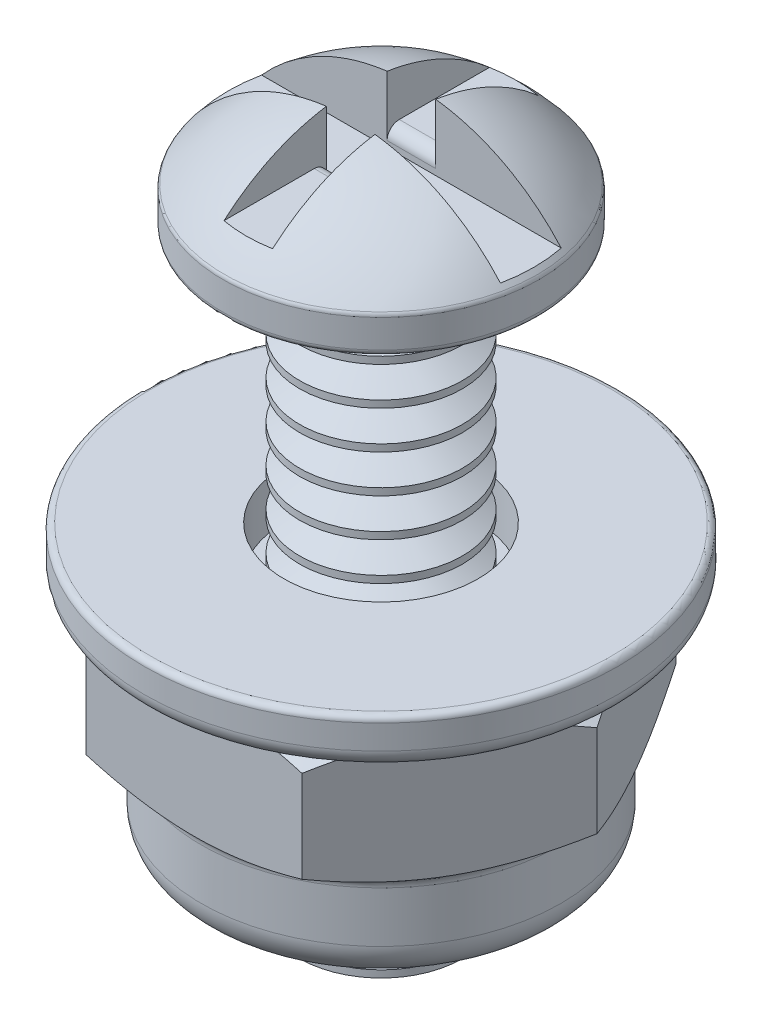
SolidWorks part; units mm, degrees
other "Nut"
other "Screw Body"
other "Washer"
material "Plain Carbon Steel"
ref_plane "Front Plane" through (0, 0, 0) normal (0, 0, 1) x (1, 0, 0)
ref_plane "Top Plane" through (0, 0, 0) normal (0, 1, 0) x (1, 0, 0)
ref_plane "Right Plane" through (0, 0, 0) normal (1, 0, 0) x (0, 0, -1)
sketch "Sketch1" plane through (0, 0, 0) normal (0, 0, 1) x (1, 0, 0)
  line L0 (0, 2.3495) -> (0, -12.7)
  line L1 (0, 0) -> (1.7018, 0) construction
  line L2 (1.7018, 0) -> (3.175, 0)
  line L3 (1.7018, 0) -> (1.7018, -12.7)
  line L4 (1.7018, -12.7) -> (0, -12.7)
  line L5 (3.302, 0.127) -> (3.302, 0.7171)
  line L6 (3.302, 0.762) -> (3.302, 2.3495) construction
  line L7 (3.302, 2.3495) -> (0, 2.3495) construction
  arc A0 (0, 2.3495) -> (3.2733, 0.7975) centre (0, -1.8783) cw
  arc A1 (3.302, 0.7171) -> (3.2733, 0.7975) centre (3.175, 0.7171) ccw
  arc A2 (3.175, 0) -> (3.302, 0.127) centre (3.175, 0.127) ccw
  point P15 (3.302, 0)
  dimension "D5" = 0.127
  dimension "D6" = 3.302
  dimension "D1" = 1.7018
  dimension "D2" = 2.3495
  dimension "D3" = 12.7
  dimension "D4" = 0.762
revolve "Revolve Screw Body" add sketch "Sketch1" angle 360 about L0
sketch "Sketch2" plane through (0, 0, 0) normal (1, 0, 0) x (0, 0, -1)
  line L0 (0, 0) -> (0, 0.889) construction
  line L2 (-0.635, 2.667) -> (0.635, 2.667)
  line L3 (-0.635, 2.667) -> (-0.635, 0.889)
  line L4 (-0.635, 0.889) -> (0.635, 0.889)
  line L5 (0.635, 2.667) -> (0.635, 0.889)
  dimension "D1" = 0.889
  dimension "D2" = 1.27
  dimension "D3" = 1.778
extrude "Long Cut Phillips" cut sketch "Sketch2" against normal through all both and the other way through all
sketch "Sketch3" plane through (0, 0, 0) normal (0, 0, 1) x (1, 0, 0)
  line L0 (0, 0) -> (0, 1.27) construction
  line L2 (-0.508, 2.54) -> (0.508, 2.54)
  line L3 (-0.508, 2.54) -> (-0.508, 1.27)
  line L4 (-0.508, 1.27) -> (0.508, 1.27)
  line L5 (0.508, 2.54) -> (0.508, 1.27)
  dimension "D1" = 1.016
  dimension "D2" = 1.27
  dimension "D3" = 1.27
extrude "Short Cut Phillips" cut sketch "Sketch3" against normal through all both and the other way through all
fillet "Phillips Fillet" radius 0.254 2 edges at (0, 1.27, 0.635) (0, 1.27, -0.635)
sketch "Sketch4" plane through (0, 0, 0) normal (0, 0, 1) x (1, 0, 0)
  line L0 (0, -12.7) -> (0, 0) construction
  line L1 (-1.7018, -12.7) -> (1.7018, -12.7) construction
  line L2 (0, -12.7) -> (1.143, -12.7) construction
  line L3 (1.143, -12.7) -> (1.8304, -12.7) construction
  line L4 (1.8304, -12.7) -> (2.6242, -12.7) construction
  line L5 (2.6242, -12.3031) -> (2.6242, -13.0969)
  line L6 (1.8304, -12.3031) -> (1.8304, -13.0969) construction
  line L7 (2.6242, -12.3031) -> (1.8304, -12.3031)
  line L8 (1.8304, -12.3031) -> (1.143, -12.7)
  line L9 (1.143, -12.7) -> (1.8304, -13.0969)
  line L10 (1.8304, -13.0969) -> (2.6242, -13.0969)
  dimension "D1" = 0.7937
  dimension "D2" = 60
  dimension "D3" = 1.143
revolve "Cut Threading" cut sketch "Sketch4" angle 360 about L0
pattern_linear "LPattern Threads" count 16 spacing 0.7937 along (0, 1, 0) of "Cut Threading"
ref_plane "Plane Nut to Head Gap" through (0, -6.35, 0) normal (0, -1, 0) x (-1, 0, 0)
sketch "Sketch5" plane through (0, -6.35, 0) normal (0, -1, 0) x (-1, 0, 0)
  line L1 (-4.5167, 0) -> (-2.2584, -3.9116)
  line L2 (-2.2584, -3.9116) -> (2.2584, -3.9116)
  line L3 (2.2584, -3.9116) -> (4.5167, 0)
  line L4 (4.5167, 0) -> (2.2584, 3.9116)
  line L5 (2.2584, 3.9116) -> (-2.2584, 3.9116)
  line L6 (-2.2584, 3.9116) -> (-4.5167, 0)
  circle A0 centre (0, 0) radius 3.9116 construction
  circle A1 centre (0, 0) radius 1.3525
  dimension "D1" = 7.8232
  dimension "D2" = 2.7051
extrude "Nut Tap Hole #36 Drill 0.1065" add sketch "Sketch5" along normal blind 2.794 separate body
sketch "Sketch6" plane through (0, 0, 0) normal (0, 0, 1) x (1, 0, 0)
  line L0 (0, -6.35) -> (0, -9.144) construction
  line L1 (2.2584, -6.35) -> (-2.2584, -6.35) construction
  line L2 (2.2584, -9.144) -> (-2.2584, -9.144) construction
  line L3 (0, -9.144) -> (3.7592, -9.144) construction
  line L4 (4.5167, -9.144) -> (2.2584, -9.144) construction
  line L5 (3.7592, -9.144) -> (3.7592, -6.35) construction
  line L6 (4.5167, -6.35) -> (2.2584, -6.35) construction
  line L7 (3.7592, -6.35) -> (0, -6.35) construction
  line L8 (3.7592, -6.35) -> (4.5167, -6.35)
  line L9 (4.5167, -6.35) -> (4.5167, -6.7874)
  line L10 (4.5167, -9.144) -> (4.5167, -6.35) construction
  line L11 (4.5167, -6.7874) -> (3.7592, -6.35)
  line L12 (3.7592, -9.144) -> (4.5167, -9.144)
  line L13 (4.5167, -9.144) -> (4.5167, -8.7066)
  line L14 (4.5167, -8.7066) -> (3.7592, -9.144)
  dimension "D1" = 30
  dimension "D2" = 3.7592
revolve "Nut Angle Edges" cut sketch "Sketch6" angle 360 about L0
sketch "Sketch8" plane through (0, -9.144, 0) normal (0, -1, 0) x (1, 0, 0)
  circle A0 centre (0, 0) radius 1.3525 construction
  circle A1 centre (0, 0) radius 1.3525
  circle A2 centre (0, 0) radius 3.7592 construction
  circle A3 centre (0, 0) radius 3.7592
extrude "Lock Nut Extrude" add sketch "Sketch8" along normal offset from surface (1.9685 mm away) 4.7625 up to face at (-3.7592, -6.35, 0)
sketch "Sketch9" plane through (0, -11.1125, 0) normal (0, -1, 0) x (1, 0, 0)
  circle A0 centre (0, 0) radius 1.778
  dimension "D1" = 3.556
extrude "Lock Nut Cut" cut sketch "Sketch9" against normal blind 0.508
fillet "Lock Nut Fillet-1" radius 0.762 1 edges at (0, -11.1125, -3.7592)
fillet "Lock Nut Fillet-2" radius 0.254 2 edges at (0, -11.1125, -1.778) (0, -9.144, -3.7592)
sketch "Sketch7" plane through (0, -6.35, 0) normal (0, -1, 0) x (1, 0, 0)
  circle A0 centre (0, 0) radius 4.953
  circle A1 centre (0, 0) radius 2.032
  dimension "D1" = 4.064
  dimension "D2" = 9.906
extrude "Washer" add sketch "Sketch7" against normal blind 1.016 separate body
fillet "Washer Fillet-1" radius 0.381 1 edges at (0, -6.35, -4.953)
fillet "Washer Fillet-2" radius 0.127 1 edges at (0, -5.334, -4.953)
